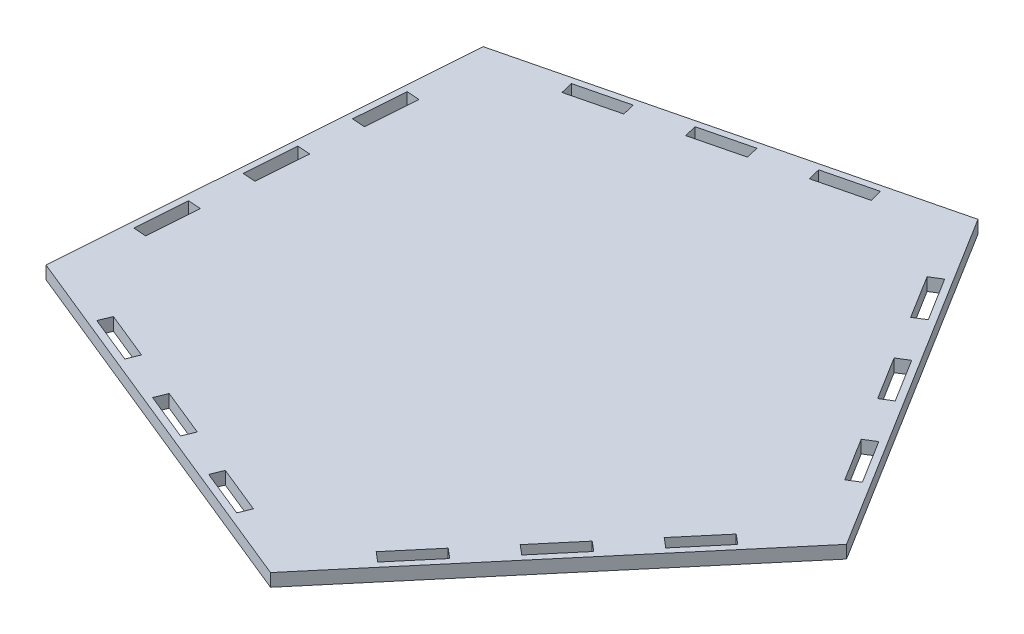
SolidWorks part; units mm, degrees
ref_plane "Front Plane" through (0, 0, 0) normal (0, 0, 1) x (1, 0, 0)
ref_plane "Top Plane" through (0, 0, 0) normal (0, 1, 0) x (1, 0, 0)
ref_plane "Right Plane" through (0, 0, 0) normal (1, 0, 0) x (0, 0, -1)
sketch "Sketch1" plane through (0, 0, 0) normal (0, 1, 0) x (1, 0, 0)
  line L1 (-472.7621, -38.6016) -> (-579.997, 133.9989)
  line L2 (-579.997, 133.9989) -> (-777.2872, 85.3489)
  line L3 (-777.2872, 85.3489) -> (-791.9844, -117.3188)
  line L4 (-791.9844, -117.3188) -> (-603.7775, -193.9245)
  line L5 (-603.7775, -193.9245) -> (-472.7621, -38.6016)
  circle A0 centre (-645.1616, -26.0994) radius 139.8404 construction
  dimension "D1" = 203.2
extrude "Boss-Extrude1" add sketch "Sketch1" along normal blind 6.35
sketch "Sketch2" plane through (0, 6.35, 0) normal (0, 1, 0) x (1, 0, 0)
  line L1 (-659.0013, -161.163) -> (-635.4754, -170.7387)
  line L2 (-659.0013, -161.163) -> (-661.3952, -167.0445)
  line L3 (-661.3952, -167.0445) -> (-637.8693, -176.6202)
  line L4 (-635.4754, -170.7387) -> (-637.8693, -176.6202)
  line L5 (-706.053, -142.0116) -> (-682.5271, -151.5873)
  line L6 (-791.9844, -117.3188) -> (-603.7775, -193.9245) construction
  line L7 (-753.0539, -122.7353) -> (-729.528, -132.311)
  line L8 (-753.0539, -122.7353) -> (-755.4478, -128.6168)
  line L9 (-755.4478, -128.6168) -> (-731.9219, -138.1925)
  line L10 (-729.528, -132.311) -> (-731.9219, -138.1925)
  line L11 (-706.053, -142.0116) -> (-708.4469, -147.8931)
  line L12 (-708.4469, -147.8931) -> (-684.921, -157.4688)
  line L13 (-682.5271, -151.5873) -> (-684.921, -157.4688)
  dimension "D1" = 3.175
  dimension "D2" = 6.35
  dimension "D3" = 25.4
  dimension "D4" = 38.1
  dimension "D5" = 25.4
  dimension "D6" = 6.35
  dimension "D7" = 38.1
  dimension "D8" = 3.175
  dimension "D9" = 6.35
  dimension "D10" = 25.4
  dimension "D11" = 25.4
extrude "Cut-Extrude1" cut sketch "Sketch2" against normal through all
sketch "Sketch4" plane through (0, 6.35, 0) normal (0, 1, 0) x (1, 0, 0)
  line L0 (-603.7775, -193.9245) -> (-472.7621, -38.6016) construction
  line L1 (-570.116, -139.2447) -> (-565.2621, -143.339)
  line L2 (-570.116, -139.2447) -> (-586.4929, -158.6601)
  line L3 (-586.4929, -158.6601) -> (-581.639, -162.7543)
  line L4 (-565.2621, -143.339) -> (-581.639, -162.7543)
  line L6 (-520.9852, -80.9987) -> (-516.1313, -85.0929)
  line L7 (-520.9852, -80.9987) -> (-504.6082, -61.5833)
  line L8 (-504.6082, -61.5833) -> (-499.7544, -65.6775)
  line L9 (-516.1313, -85.0929) -> (-499.7544, -65.6775)
  line L10 (-548.8852, -123.9236) -> (-532.5083, -104.5082)
  line L11 (-548.8852, -123.9236) -> (-553.739, -119.8294)
  line L12 (-553.739, -119.8294) -> (-537.3621, -100.414)
  line L13 (-532.5083, -104.5082) -> (-537.3621, -100.414)
  dimension "D1" = 6.35
  dimension "D2" = 25.4
  dimension "D3" = 3.175
  dimension "D4" = 38.1
  dimension "D5" = 3.175
  dimension "D6" = 6.35
  dimension "D7" = 25.4
  dimension "D8" = 38.1
  dimension "D9" = 6.35
  dimension "D10" = 25.4
  dimension "D11" = 3.175
  dimension "D12" = 25.4
extrude "Cut-Extrude2" cut sketch "Sketch4" against normal through all
sketch "Sketch5" plane through (0, 6.35, 0) normal (0, 1, 0) x (1, 0, 0)
  line L0 (-777.2872, 85.3489) -> (-791.9844, -117.3188) construction
  line L1 (-777.8914, -54.6741) -> (-784.2248, -54.2148)
  line L2 (-777.8914, -54.6741) -> (-779.7286, -80.0076)
  line L3 (-779.7286, -80.0076) -> (-786.0619, -79.5483)
  line L4 (-784.2248, -54.2148) -> (-786.0619, -79.5483)
  line L6 (-774.2171, -4.0071) -> (-780.5505, -3.5479)
  line L7 (-774.2171, -4.0071) -> (-776.0543, -29.3406)
  line L8 (-776.0543, -29.3406) -> (-782.3876, -28.8813)
  line L9 (-780.5505, -3.5479) -> (-782.3876, -28.8813)
  line L10 (-776.8762, 47.1191) -> (-770.5428, 46.6598)
  line L11 (-776.8762, 47.1191) -> (-778.7133, 21.7856)
  line L12 (-778.7133, 21.7856) -> (-772.38, 21.3263)
  line L13 (-770.5428, 46.6598) -> (-772.38, 21.3263)
  dimension "D1" = 6.35
  dimension "D2" = 25.4
  dimension "D3" = 3.175
  dimension "D4" = 38.1
  dimension "D5" = 25.4
  dimension "D6" = 6.35
  dimension "D7" = 3.175
  dimension "D8" = 25.4
  dimension "D9" = 6.35
  dimension "D10" = 25.4
  dimension "D11" = 3.175
  dimension "D12" = 38.1
extrude "Cut-Extrude3" cut sketch "Sketch5" against normal through all
sketch "Sketch6" plane through (0, 6.35, 0) normal (0, 1, 0) x (1, 0, 0)
  line L0 (-472.7621, -38.6016) -> (-579.997, 133.9989) construction
  line L1 (-508.9699, 13.6605) -> (-495.5655, -7.9146)
  line L2 (-508.9699, 13.6605) -> (-514.3636, 10.3094)
  line L3 (-514.3636, 10.3094) -> (-500.9593, -11.2656)
  line L4 (-495.5655, -7.9146) -> (-500.9593, -11.2656)
  line L6 (-522.3742, 35.2356) -> (-527.768, 31.8845)
  line L7 (-522.3742, 35.2356) -> (-535.7786, 56.8106)
  line L8 (-535.7786, 56.8106) -> (-541.1724, 53.4595)
  line L9 (-527.768, 31.8845) -> (-541.1724, 53.4595)
  line L10 (-549.1398, 78.4125) -> (-554.5336, 75.0614)
  line L11 (-549.1398, 78.4125) -> (-562.5442, 99.9876)
  line L12 (-562.5442, 99.9876) -> (-567.9379, 96.6365)
  line L13 (-554.5336, 75.0614) -> (-567.9379, 96.6365)
  dimension "D1" = 6.35
  dimension "D2" = 25.4
  dimension "D3" = 3.175
  dimension "D4" = 38.1
  dimension "D5" = 6.35
  dimension "D6" = 25.4
  dimension "D7" = 3.175
  dimension "D8" = 25.4
  dimension "D9" = 25.4
  dimension "D10" = 6.35
  dimension "D11" = 3.1242
  dimension "D12" = 38.1
extrude "Cut-Extrude4" cut sketch "Sketch6" against normal through all
sketch "Sketch7" plane through (0, 6.35, 0) normal (0, 1, 0) x (1, 0, 0)
  line L0 (-579.997, 133.9989) -> (-777.2872, 85.3489) construction
  line L1 (-614.7084, 115.629) -> (-639.3697, 109.5478)
  line L2 (-614.7084, 115.629) -> (-616.2287, 121.7944)
  line L3 (-616.2287, 121.7944) -> (-640.89, 115.7131)
  line L4 (-639.3697, 109.5478) -> (-640.89, 115.7131)
  line L6 (-665.5513, 109.6319) -> (-690.2125, 103.5506)
  line L7 (-665.5513, 109.6319) -> (-664.031, 103.4666)
  line L8 (-664.031, 103.4666) -> (-688.6922, 97.3853)
  line L9 (-690.2125, 103.5506) -> (-688.6922, 97.3853)
  line L10 (-714.8738, 97.4694) -> (-739.5351, 91.3882)
  line L11 (-714.8738, 97.4694) -> (-713.3535, 91.3041)
  line L12 (-713.3535, 91.3041) -> (-738.0148, 85.2228)
  line L13 (-739.5351, 91.3882) -> (-738.0148, 85.2228)
  point P7 (-615.4686, 118.7117)
  dimension "D1" = 25.4
  dimension "D2" = 6.35
  dimension "D3" = 3.175
  dimension "D4" = 38.1
  dimension "D5" = 6.35
  dimension "D6" = 25.4
  dimension "D7" = 3.175
  dimension "D8" = 25.4
  dimension "D9" = 25.4
  dimension "D10" = 6.35
  dimension "D11" = 3.175
  dimension "D12" = 25.4
extrude "Cut-Extrude5" cut sketch "Sketch7" against normal through all
sketch "Sketch11" plane through (0, 6.35, 0) normal (0, 1, 0) x (1, 0, 0)
  line L14 (-784.0368, -54.4322) -> (-785.8446, -79.3603)
  line L15 (-785.8446, -79.3603) -> (-779.9165, -79.7902)
  line L16 (-779.9165, -79.7902) -> (-778.1088, -54.8621)
  line L17 (-778.1088, -54.8621) -> (-784.0368, -54.4322)
  line L18 (-784.0368, -54.4322) -> (-785.8446, -79.3603)
  line L19 (-785.8446, -79.3603) -> (-779.9165, -79.7902)
  line L20 (-779.9165, -79.7902) -> (-778.1088, -54.8621)
  line L21 (-778.1088, -54.8621) -> (-784.0368, -54.4322)
  line L22 (-553.4527, -119.8051) -> (-548.9095, -123.6373)
  line L23 (-548.9095, -123.6373) -> (-532.7946, -104.5326)
  line L24 (-532.7946, -104.5326) -> (-537.3378, -100.7004)
  line L25 (-537.3378, -100.7004) -> (-553.4527, -119.8051)
  line L26 (-553.4527, -119.8051) -> (-548.9095, -123.6373)
  line L27 (-548.9095, -123.6373) -> (-532.7946, -104.5326)
  line L28 (-532.7946, -104.5326) -> (-537.3378, -100.7004)
  line L29 (-537.3378, -100.7004) -> (-553.4527, -119.8051)
  line L32 (-780.3625, -3.7652) -> (-782.1703, -28.6934)
  line L33 (-774.4345, -4.1951) -> (-780.3625, -3.7652)
  line L34 (-776.2422, -29.1232) -> (-774.4345, -4.1951)
  line L35 (-782.1703, -28.6934) -> (-776.2422, -29.1232)
  line L36 (-780.3625, -3.7652) -> (-782.1703, -28.6934)
  line L37 (-774.4345, -4.1951) -> (-780.3625, -3.7652)
  line L38 (-776.2422, -29.1232) -> (-774.4345, -4.1951)
  line L39 (-782.1703, -28.6934) -> (-776.2422, -29.1232)
  line L41 (-685.0326, -157.204) -> (-682.7919, -151.6989)
  line L42 (-708.1821, -147.7815) -> (-685.0326, -157.204)
  line L43 (-682.7919, -151.6989) -> (-705.9414, -142.2764)
  line L44 (-705.9414, -142.2764) -> (-708.1821, -147.7815)
  line L45 (-685.0326, -157.204) -> (-682.7919, -151.6989)
  line L46 (-708.1821, -147.7815) -> (-685.0326, -157.204)
  line L47 (-682.7919, -151.6989) -> (-705.9414, -142.2764)
  line L48 (-565.5485, -143.3633) -> (-570.0917, -139.5311)
  line L49 (-586.2065, -158.6358) -> (-581.6634, -162.468)
  line L50 (-770.7602, 46.4718) -> (-776.6882, 46.9017)
  line L51 (-778.496, 21.9736) -> (-772.568, 21.5437)
  line L52 (-772.568, 21.5437) -> (-770.7602, 46.4718)
  line L53 (-776.6882, 46.9017) -> (-778.496, 21.9736)
  line L54 (-770.7602, 46.4718) -> (-776.6882, 46.9017)
  line L55 (-778.496, 21.9736) -> (-772.568, 21.5437)
  line L56 (-772.568, 21.5437) -> (-770.7602, 46.4718)
  line L57 (-776.6882, 46.9017) -> (-778.496, 21.9736)
  line L58 (-581.6634, -162.468) -> (-565.5485, -143.3633)
  line L59 (-570.0917, -139.5311) -> (-586.2065, -158.6358)
  line L60 (-565.5485, -143.3633) -> (-570.0917, -139.5311)
  line L61 (-586.2065, -158.6358) -> (-581.6634, -162.468)
  line L62 (-581.6634, -162.468) -> (-565.5485, -143.3633)
  line L63 (-570.0917, -139.5311) -> (-586.2065, -158.6358)
  line L64 (-705.9414, -142.2764) -> (-708.1821, -147.7815)
  line L68 (-713.5994, 91.4527) -> (-715.0225, 97.2235)
  line L69 (-739.2892, 91.2395) -> (-737.8661, 85.4688)
  line L70 (-737.8661, 85.4688) -> (-713.5994, 91.4527)
  line L71 (-715.0225, 97.2235) -> (-739.2892, 91.2395)
  line L72 (-713.5994, 91.4527) -> (-715.0225, 97.2235)
  line L73 (-739.2892, 91.2395) -> (-737.8661, 85.4688)
  line L74 (-737.8661, 85.4688) -> (-713.5994, 91.4527)
  line L75 (-715.0225, 97.2235) -> (-739.2892, 91.2395)
  line L82 (-658.8897, -161.4278) -> (-661.1304, -166.9329)
  line L83 (-637.9809, -176.3554) -> (-635.7402, -170.8503)
  line L84 (-635.7402, -170.8503) -> (-658.8897, -161.4278)
  line L85 (-661.1304, -166.9329) -> (-637.9809, -176.3554)
  line L86 (-664.2769, 103.6152) -> (-665.6999, 109.3859)
  line L87 (-689.9666, 103.402) -> (-688.5436, 97.6313)
  line L88 (-688.5436, 97.6313) -> (-664.2769, 103.6152)
  line L89 (-665.6999, 109.3859) -> (-689.9666, 103.402)
  line L90 (-664.2769, 103.6152) -> (-665.6999, 109.3859)
  line L91 (-689.9666, 103.402) -> (-688.5436, 97.6313)
  line L92 (-688.5436, 97.6313) -> (-664.2769, 103.6152)
  line L93 (-665.6999, 109.3859) -> (-689.9666, 103.402)
  line L94 (-658.8897, -161.4278) -> (-661.1304, -166.9329)
  line L95 (-637.9809, -176.3554) -> (-635.7402, -170.8503)
  line L96 (-635.7402, -170.8503) -> (-658.8897, -161.4278)
  line L97 (-661.1304, -166.9329) -> (-637.9809, -176.3554)
  line L104 (-614.9543, 115.7777) -> (-616.3774, 121.5484)
  line L105 (-640.6441, 115.5645) -> (-639.221, 109.7937)
  line L106 (-639.221, 109.7937) -> (-614.9543, 115.7777)
  line L107 (-616.3774, 121.5484) -> (-640.6441, 115.5645)
  line L108 (-614.9543, 115.7777) -> (-616.3774, 121.5484)
  line L109 (-640.6441, 115.5645) -> (-639.221, 109.7937)
  line L110 (-639.221, 109.7937) -> (-614.9543, 115.7777)
  line L111 (-616.3774, 121.5484) -> (-640.6441, 115.5645)
  line L116 (-752.9423, -123.0001) -> (-755.183, -128.5052)
  line L117 (-732.0335, -137.9277) -> (-729.7928, -132.4226)
  line L118 (-729.7928, -132.4226) -> (-752.9423, -123.0001)
  line L119 (-755.183, -128.5052) -> (-732.0335, -137.9277)
  line L120 (-752.9423, -123.0001) -> (-755.183, -128.5052)
  line L121 (-732.0335, -137.9277) -> (-729.7928, -132.4226)
  line L122 (-554.4682, 75.3412) -> (-549.4196, 78.4779)
  line L123 (-562.6095, 99.7077) -> (-567.6581, 96.5711)
  line L124 (-549.4196, 78.4779) -> (-562.6095, 99.7077)
  line L125 (-567.6581, 96.5711) -> (-554.4682, 75.3412)
  line L126 (-554.4682, 75.3412) -> (-549.4196, 78.4779)
  line L127 (-562.6095, 99.7077) -> (-567.6581, 96.5711)
  line L128 (-549.4196, 78.4779) -> (-562.6095, 99.7077)
  line L129 (-567.6581, 96.5711) -> (-554.4682, 75.3412)
  line L130 (-729.7928, -132.4226) -> (-752.9423, -123.0001)
  line L131 (-755.183, -128.5052) -> (-732.0335, -137.9277)
  line L140 (-527.7026, 32.1643) -> (-522.6541, 35.3009)
  line L141 (-522.6541, 35.3009) -> (-535.844, 56.5308)
  line L142 (-535.844, 56.5308) -> (-540.8925, 53.3942)
  line L143 (-540.8925, 53.3942) -> (-527.7026, 32.1643)
  line L144 (-527.7026, 32.1643) -> (-522.6541, 35.3009)
  line L145 (-522.6541, 35.3009) -> (-535.844, 56.5308)
  line L146 (-535.844, 56.5308) -> (-540.8925, 53.3942)
  line L147 (-540.8925, 53.3942) -> (-527.7026, 32.1643)
  line L156 (-579.9023, 134.2315) -> (-777.4792, 85.5109)
  line L157 (-472.5116, -38.6198) -> (-579.9023, 134.2315)
  line L158 (-500.8939, -10.9858) -> (-495.8454, -7.8492)
  line L159 (-514.0838, 10.2441) -> (-500.8939, -10.9858)
  line L160 (-495.8454, -7.8492) -> (-509.0352, 13.3807)
  line L161 (-509.0352, 13.3807) -> (-514.0838, 10.2441)
  line L162 (-500.8939, -10.9858) -> (-495.8454, -7.8492)
  line L163 (-514.0838, 10.2441) -> (-500.8939, -10.9858)
  line L164 (-495.8454, -7.8492) -> (-509.0352, 13.3807)
  line L165 (-509.0352, 13.3807) -> (-514.0838, 10.2441)
  line L166 (-603.7174, -194.1684) -> (-472.5116, -38.6198)
  line L167 (-777.4792, 85.5109) -> (-792.1977, -117.4514)
  line L168 (-792.1977, -117.4514) -> (-603.7174, -194.1684)
  line L169 (-579.9023, 134.2315) -> (-777.4792, 85.5109)
  line L170 (-472.5116, -38.6198) -> (-579.9023, 134.2315)
  line L171 (-603.7174, -194.1684) -> (-472.5116, -38.6198)
  line L172 (-777.4792, 85.5109) -> (-792.1977, -117.4514)
  line L173 (-792.1977, -117.4514) -> (-603.7174, -194.1684)
  line L176 (-520.6988, -80.9743) -> (-516.1556, -84.8065)
  line L177 (-516.1556, -84.8065) -> (-500.0407, -65.7018)
  line L178 (-500.0407, -65.7018) -> (-504.5839, -61.8696)
  line L179 (-504.5839, -61.8696) -> (-520.6988, -80.9743)
  line L180 (-520.6988, -80.9743) -> (-516.1556, -84.8065)
  line L181 (-516.1556, -84.8065) -> (-500.0407, -65.7018)
  line L182 (-500.0407, -65.7018) -> (-504.5839, -61.8696)
  line L183 (-504.5839, -61.8696) -> (-520.6988, -80.9743)
  dimension "D1" = 0.2032
  dimension "D2" = 0.2032
  dimension "D3" = 0.2032
  dimension "D4" = 0.2032
  dimension "D5" = 0.2032
  dimension "D6" = 0.2032
  dimension "D7" = 0.2032
  dimension "D8" = 0.2032
  dimension "D9" = 0.2032
  dimension "D10" = 0.2032
  dimension "D11" = 0.2032
  dimension "D12" = 0.2032
  dimension "D13" = 0.2032
  dimension "D14" = 0.2032
  dimension "D15" = 0.2032
  dimension "D16" = 0.2032
